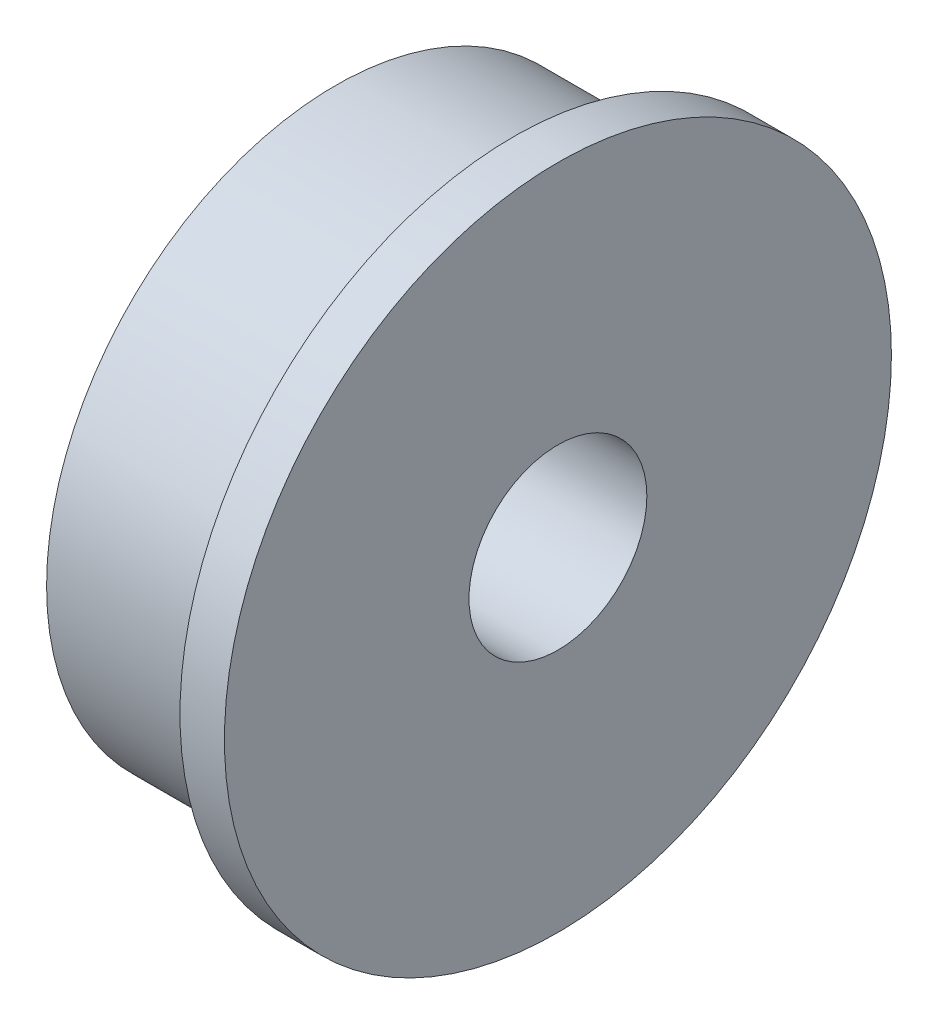
SolidWorks part; units mm, degrees
ref_plane "Front Plane" through (0, 0, 0) normal (0, 0, 1) x (1, 0, 0)
ref_plane "Top Plane" through (0, 0, 0) normal (0, 1, 0) x (1, 0, 0)
ref_plane "Right Plane" through (0, 0, 0) normal (1, 0, 0) x (0, 0, -1)
sketch "Sketch1" plane through (0, 0, 0) normal (0, 0, 1) x (1, 0, 0)
  line L0 (-0.5852, 7.5) -> (-1.5852, 7.5)
  line L1 (-1.5852, 7.5) -> (-1.5852, 6.5)
  line L2 (-1.5852, 6.5) -> (-5.5852, 6.5)
  line L3 (-5.5852, 6.5) -> (-5.5852, 2)
  line L4 (-5.5852, 2) -> (-0.5852, 2)
  line L5 (-0.5852, 2) -> (-0.5852, 7.5)
  line L6 (0, 0) -> (-6.3556, 0) construction
  dimension "D1" = 2
  dimension "D2" = 1
  dimension "D3" = 5
  dimension "D4" = 6.5
  dimension "2" = 7.5
revolve "Revolve1" add sketch "Sketch1" angle 360 about L6
